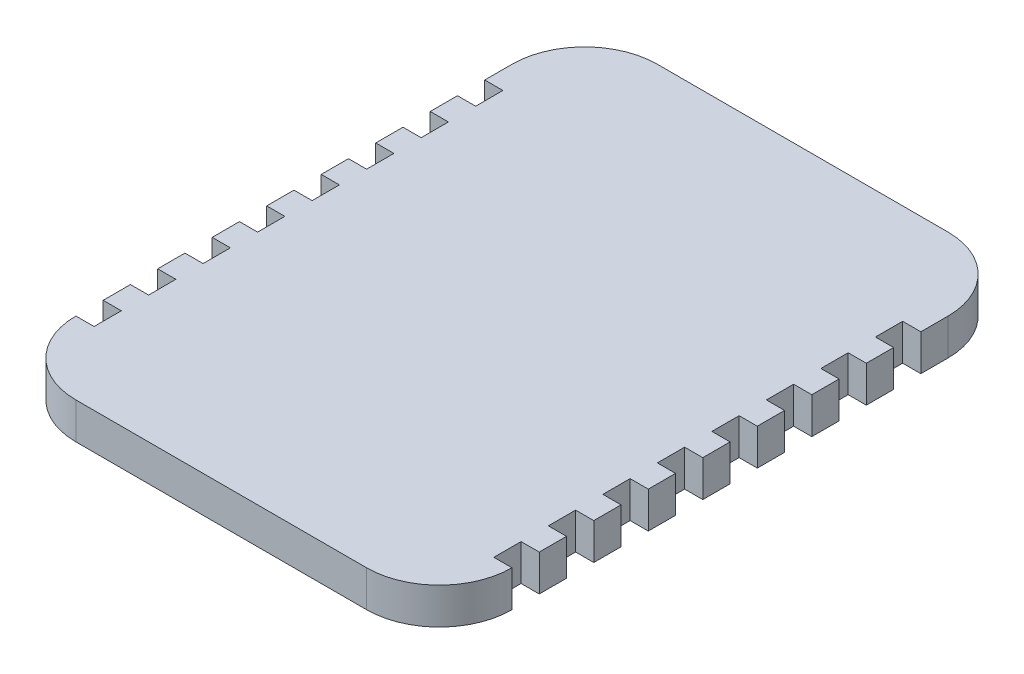
SolidWorks part; units mm, degrees
ref_plane "Front Plane" through (0, 0, 0) normal (0, 0, 1) x (1, 0, 0)
ref_plane "Top Plane" through (0, 0, 0) normal (0, 1, 0) x (1, 0, 0)
ref_plane "Right Plane" through (0, 0, 0) normal (1, 0, 0) x (0, 0, -1)
sketch "Sketch1" plane through (0, 0, 0) normal (0, 1, 0) x (1, 0, 0)
  line L0 (356.5379, 539.6819) -> (1600.9879, 539.6819) construction
  line L1 (-10, 30) -> (-10, 270)
  line L6 (30, 310) -> (190, 310)
  line L7 (230, 30) -> (230, 270)
  line L8 (30, -10) -> (190, -10)
  arc A4 (30, 310) -> (-10, 270) centre (30, 270) ccw
  arc A5 (190, 310) -> (230, 270) centre (190, 270) cw
  arc A6 (230, 30) -> (190, -10) centre (190, 30) cw
  arc A7 (-10, 30) -> (30, -10) centre (30, 30) ccw
  point P2 (0, 0)
  point P3 (0, 0)
  point P13 (220, 0)
  point P16 (0, 0)
  dimension "D1" = 320
  dimension "D2" = 220
extrude "Boss-Extrude1" add sketch "Sketch1" along normal blind 20
sketch "Sketch3" plane through (-10, 0, 0) normal (-1, 0, 0) x (0, 0, 1)
  line L0 (-270, 20) -> (-30, 20) construction
  line L1 (-270, 0) -> (-255, 0)
  line L2 (-270, 0) -> (-270, 20)
  line L3 (-270, 20) -> (-255, 20)
  line L4 (-255, 0) -> (-255, 20)
  line L5 (-255, 0) -> (-255, 20)
  line L6 (-255, 0) -> (-240, 0)
  line L7 (-240, 0) -> (-240, 20)
  line L8 (-255, 20) -> (-240, 20)
  line L9 (-240, 0) -> (-240, 20)
  line L10 (-240, 0) -> (-225, 0)
  line L11 (-225, 0) -> (-225, 20)
  line L12 (-240, 20) -> (-225, 20)
  line L13 (-225, 0) -> (-225, 20)
  line L14 (-225, 0) -> (-210, 0)
  line L15 (-210, 0) -> (-210, 20)
  line L16 (-225, 20) -> (-210, 20)
  line L17 (-210, 0) -> (-210, 20)
  line L18 (-210, 0) -> (-195, 0)
  line L19 (-195, 0) -> (-195, 20)
  line L20 (-210, 20) -> (-195, 20)
  line L21 (-195, 0) -> (-195, 20)
  line L22 (-195, 0) -> (-180, 0)
  line L23 (-180, 0) -> (-180, 20)
  line L24 (-195, 20) -> (-180, 20)
  line L25 (-180, 0) -> (-180, 20)
  line L26 (-180, 0) -> (-165, 0)
  line L27 (-165, 0) -> (-165, 20)
  line L28 (-180, 20) -> (-165, 20)
  line L29 (-165, 0) -> (-165, 20)
  line L30 (-165, 0) -> (-150, 0)
  line L31 (-150, 0) -> (-150, 20)
  line L32 (-165, 20) -> (-150, 20)
  line L33 (-150, 0) -> (-150, 20)
  line L34 (-150, 0) -> (-135, 0)
  line L35 (-135, 0) -> (-135, 20)
  line L36 (-150, 20) -> (-135, 20)
  line L37 (-135, 0) -> (-135, 20)
  line L38 (-135, 0) -> (-120, 0)
  line L39 (-120, 0) -> (-120, 20)
  line L40 (-135, 20) -> (-120, 20)
  line L41 (-120, 0) -> (-120, 20)
  line L42 (-120, 0) -> (-105, 0)
  line L43 (-105, 0) -> (-105, 20)
  line L44 (-120, 20) -> (-105, 20)
  line L45 (-105, 0) -> (-105, 20)
  line L46 (-105, 0) -> (-90, 0)
  line L47 (-90, 0) -> (-90, 20)
  line L48 (-105, 20) -> (-90, 20)
  line L49 (-90, 0) -> (-90, 20)
  line L50 (-90, 0) -> (-75, 0)
  line L51 (-75, 0) -> (-75, 20)
  line L52 (-90, 20) -> (-75, 20)
  line L53 (-75, 0) -> (-75, 20)
  line L54 (-75, 0) -> (-60, 0)
  line L55 (-60, 0) -> (-60, 20)
  line L56 (-75, 20) -> (-60, 20)
  line L57 (-60, 0) -> (-60, 20)
  line L58 (-60, 0) -> (-45, 0)
  line L59 (-45, 0) -> (-45, 20)
  line L60 (-60, 20) -> (-45, 20)
  line L61 (-45, 0) -> (-45, 20)
  line L62 (-45, 0) -> (-30, 0)
  line L63 (-30, 0) -> (-30, 20)
  line L64 (-45, 20) -> (-30, 20)
  line M3 (-270, 0) -> (-30, 0)
  line M4 (-30, 0) -> (-30, 20)
  line M5 (-30, 20) -> (-270, 20)
  dimension "D1" = 15
  dimension "D2" = 16
sketch "Sketch4" plane through (230, 0, 0) normal (1, 0, 0) x (0, 0, -1)
  line L0 (30, 20) -> (270, 20) construction
  line L1 (270, 0) -> (255, 0)
  line L2 (270, 0) -> (270, 20)
  line L3 (270, 20) -> (255, 20)
  line L4 (255, 0) -> (255, 20)
  line L5 (255, 0) -> (255, 20)
  line L6 (255, 0) -> (240, 0)
  line L7 (240, 0) -> (240, 20)
  line L8 (255, 20) -> (240, 20)
  line L9 (240, 0) -> (240, 20)
  line L10 (240, 0) -> (225, 0)
  line L11 (225, 0) -> (225, 20)
  line L12 (240, 20) -> (225, 20)
  line L13 (225, 0) -> (225, 20)
  line L14 (225, 0) -> (210, 0)
  line L15 (210, 0) -> (210, 20)
  line L16 (225, 20) -> (210, 20)
  line L17 (210, 0) -> (210, 20)
  line L18 (210, 0) -> (195, 0)
  line L19 (195, 0) -> (195, 20)
  line L20 (210, 20) -> (195, 20)
  line L21 (195, 0) -> (195, 20)
  line L22 (195, 0) -> (180, 0)
  line L23 (180, 0) -> (180, 20)
  line L24 (195, 20) -> (180, 20)
  line L25 (180, 0) -> (180, 20)
  line L26 (180, 0) -> (165, 0)
  line L27 (165, 0) -> (165, 20)
  line L28 (180, 20) -> (165, 20)
  line L29 (165, 0) -> (165, 20)
  line L30 (165, 0) -> (150, 0)
  line L31 (150, 0) -> (150, 20)
  line L32 (165, 20) -> (150, 20)
  line L33 (150, 0) -> (150, 20)
  line L34 (150, 0) -> (135, 0)
  line L35 (135, 0) -> (135, 20)
  line L36 (150, 20) -> (135, 20)
  line L37 (135, 0) -> (135, 20)
  line L38 (135, 0) -> (120, 0)
  line L39 (120, 0) -> (120, 20)
  line L40 (135, 20) -> (120, 20)
  line L41 (120, 0) -> (120, 20)
  line L42 (120, 0) -> (105, 0)
  line L43 (105, 0) -> (105, 20)
  line L44 (120, 20) -> (105, 20)
  line L45 (105, 0) -> (105, 20)
  line L46 (105, 0) -> (90, 0)
  line L47 (90, 0) -> (90, 20)
  line L48 (105, 20) -> (90, 20)
  line L49 (90, 0) -> (90, 20)
  line L50 (90, 0) -> (75, 0)
  line L51 (75, 0) -> (75, 20)
  line L52 (90, 20) -> (75, 20)
  line L53 (75, 0) -> (75, 20)
  line L54 (75, 0) -> (60, 0)
  line L55 (60, 0) -> (60, 20)
  line L56 (75, 20) -> (60, 20)
  line L57 (60, 0) -> (60, 20)
  line L58 (60, 0) -> (45, 0)
  line L59 (45, 0) -> (45, 20)
  line L60 (60, 20) -> (45, 20)
  line L61 (45, 0) -> (45, 20)
  line L62 (45, 0) -> (30, 0)
  line L63 (30, 0) -> (30, 20)
  line L64 (45, 20) -> (30, 20)
  line M5 (30, 0) -> (270, 0)
  line M7 (270, 20) -> (30, 20)
  line M8 (30, 20) -> (30, 0)
  dimension "D1" = 15
  dimension "D2" = 16
extrude "Cut-Extrude1" cut sketch "Sketch3" against normal blind 10 contours L7 L4 M3 M5 | L15 L11 M3 M5 | L23 L19 M3 M5 | L31 L27 M3 M5 | L39 L35 M3 M5 | L47 L43 M3 M5 | L55 L51 M3 M5 | L59 M3 M4 M5
extrude "Cut-Extrude2" cut sketch "Sketch4" against normal blind 10 contours L7 L4 M5 M7 | L15 L11 M5 M7 | L31 L27 M5 M7 | L39 L35 M5 M7 | L47 L43 M5 M7 | L55 L51 M5 M7 | L59 M5 M7 M8 | L23 L19 M5 M7
